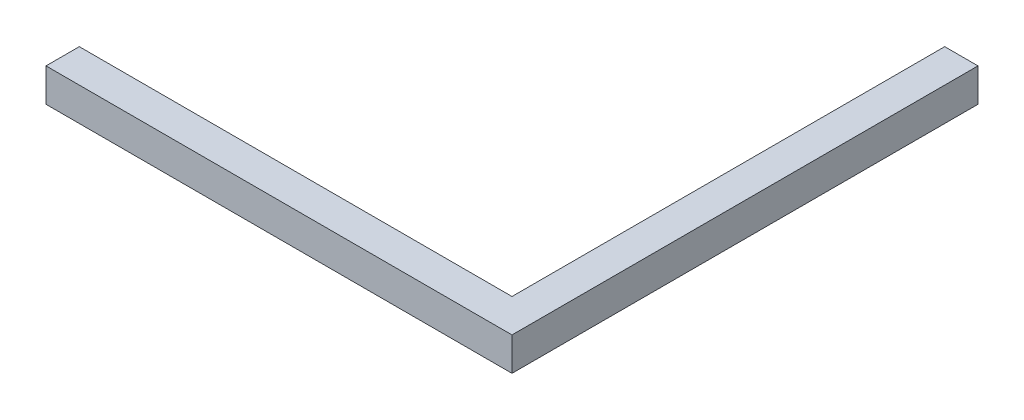
SolidWorks part; units mm, degrees
ref_plane "Front Plane" through (0, 0, 0) normal (0, 0, 1) x (1, 0, 0)
ref_plane "Top Plane" through (0, 0, 0) normal (0, 1, 0) x (1, 0, 0)
ref_plane "Right Plane" through (0, 0, 0) normal (1, 0, 0) x (0, 0, -1)
sketch "Sketch1" plane through (0, 0, 0) normal (0, 1, 0) x (1, 0, 0)
  line L0 (-70, 70) -> (70, -70) construction
  line L1 (-70, 70) -> (70, 70) construction
  line L2 (-70, 70) -> (-70, -70) construction
  line L3 (-70, -70) -> (70, -70) construction
  line L4 (70, 70) -> (70, -70) construction
  line L5 (-70, -70) -> (70, -70)
  line L6 (70, -70) -> (70, 70)
  line L7 (70, 70) -> (60, 70)
  line L8 (60, 70) -> (60, -60)
  line L9 (60, -60) -> (-70, -60)
  line L10 (-70, -60) -> (-70, -70)
  dimension "D1" = 140
  dimension "D2" = 140
  dimension "D3" = 10
  dimension "D4" = 10
extrude "Boss-Extrude1" add sketch "Sketch1" along normal blind 10
